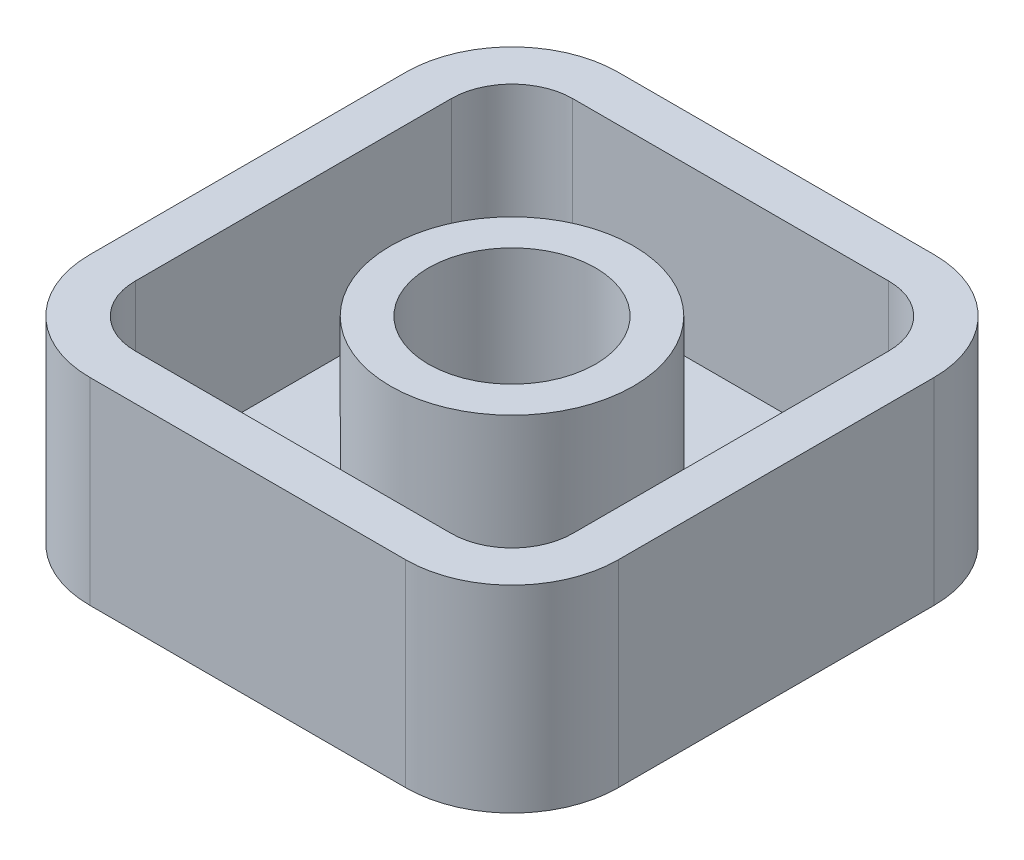
SolidWorks part; units mm, degrees
ref_plane "Front Plane" through (0, 0, 0) normal (0, 0, 1) x (1, 0, 0)
ref_plane "Top Plane" through (0, 0, 0) normal (0, 1, 0) x (1, 0, 0)
ref_plane "Right Plane" through (0, 0, 0) normal (1, 0, 0) x (0, 0, -1)
sketch "Sketch1" plane through (0, 0, 0) normal (0, 1, 0) x (1, 0, 0)
  line L1 (0, 0) -> (-17.4, 0)
  line L2 (0, 0) -> (0, -17.4)
  line L3 (0, -17.4) -> (-17.4, -17.4)
  line L4 (-17.4, 0) -> (-17.4, -17.4)
  dimension "D1" = 17.4
  dimension "D2" = 17.4
  dimension "D3" = 17.4
extrude "Boss-Extrude1" add sketch "Sketch1" along normal blind 6.5
fillet "Fillet1" radius 3.5 4 edges at (-17.4, 3.25, 17.4) (-17.4, 3.25, 0) (0, 3.25, 0) (0, 3.25, 17.4)
sketch "Sketch2" plane through (0, 6.5, 0) normal (0, 1, 0) x (1, 0, 0)
  line L0 (-3.5, 0) -> (-13.9, 0) construction
  line L1 (-13.9, -15.9) -> (-3.5, -15.9)
  line L2 (-15.9, -13.9) -> (-15.9, -3.5)
  line L3 (-13.9, -1.5) -> (-3.5, -1.5)
  line L4 (-1.5, -13.9) -> (-1.5, -3.5)
  line L5 (-15.9, -15.9) -> (-1.5, -1.5) construction
  line L6 (-15.9, -1.5) -> (-1.5, -15.9) construction
  line L7 (0, -13.9) -> (0, -3.5) construction
  line L8 (-17.4, -3.5) -> (-17.4, -13.9) construction
  line L9 (-13.9, -17.4) -> (-3.5, -17.4) construction
  arc A0 (-13.9, -15.9) -> (-15.9, -13.9) centre (-13.9, -13.9) cw
  arc A1 (-3.5, -15.9) -> (-1.5, -13.9) centre (-3.5, -13.9) ccw
  arc A2 (-3.5, -1.5) -> (-1.5, -3.5) centre (-3.5, -3.5) cw
  arc A3 (-13.9, -1.5) -> (-15.9, -3.5) centre (-13.9, -3.5) ccw
  point P0 (-8.7, -8.7)
  dimension "D5" = 2
  dimension "D1" = 1.5
  dimension "D2" = 1.5
  dimension "D3" = 1.5
  dimension "D4" = 1.5
extrude "Cut-Extrude1" cut sketch "Sketch2" against normal blind 5.5
sketch "Sketch3" plane through (0, 1, 0) normal (0, 1, 0) x (1, 0, 0)
  line L2 (0, -13.9) -> (0, -3.5) construction
  line L3 (-3.5, 0) -> (-13.9, 0) construction
  circle A0 centre (-8.7, -8.7) radius 4
  circle A1 centre (-8.7, -8.7) radius 2.75
  point P7 (-8.7, 0)
  dimension "D3" = 8
  dimension "D4" = 5.5
  dimension "D1" = 8.7
  dimension "D2" = 8.7
extrude "Boss-Extrude2" add sketch "Sketch3" along normal blind 5.5
sketch "Sketch4" plane through (0, 1, 0) normal (0, 1, 0) x (1, 0, 0)
  circle A1 centre (-8.7, -8.7) radius 2.75
  circle A3 centre (-8.7, -8.7) radius 2.75
  dimension "D1" = 0
extrude "Cut-Extrude2" cut sketch "Sketch4" against normal blind 0.4
